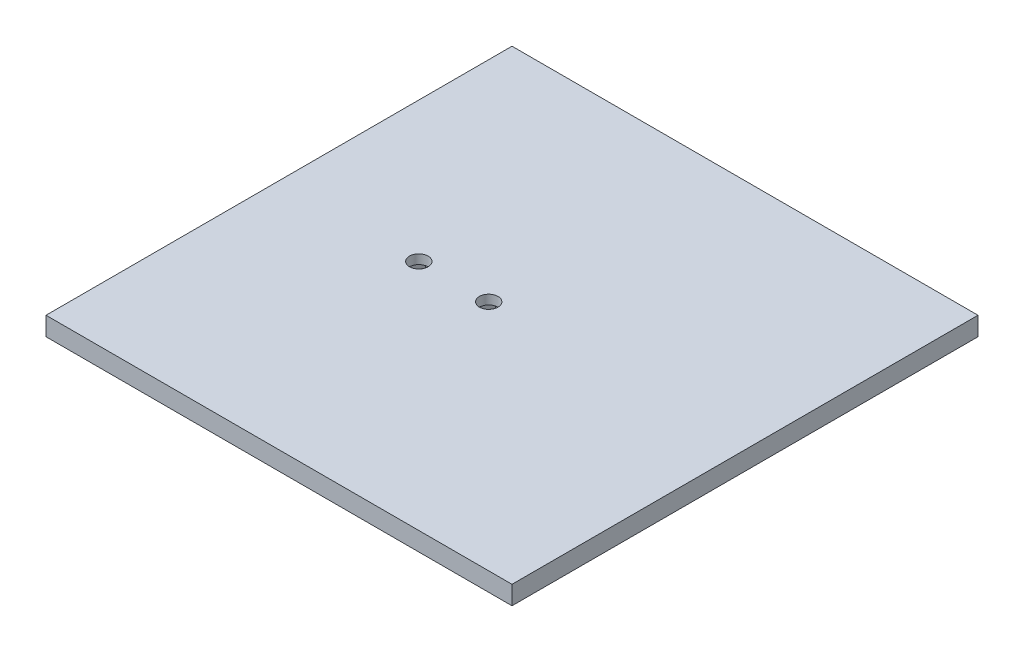
SolidWorks part; units mm, degrees
ref_plane "Front Plane" through (0, 0, 0) normal (0, 0, 1) x (1, 0, 0)
ref_plane "Top Plane" through (0, 0, 0) normal (0, 1, 0) x (1, 0, 0)
ref_plane "Right Plane" through (0, 0, 0) normal (1, 0, 0) x (0, 0, -1)
sketch "Sketch1" plane through (0, 0, 0) normal (0, 1, 0) x (1, 0, 0)
  line L1 (-34.8765, 23.534) -> (65.1235, 23.534)
  line L2 (-34.8765, 23.534) -> (-34.8765, -76.466)
  line L3 (-34.8765, -76.466) -> (65.1235, -76.466)
  line L4 (65.1235, 23.534) -> (65.1235, -76.466)
  point P22 (2.0874, -26.3153)
  dimension "D1" = 100
  dimension "D2" = 100
extrude "Boss-Extrude1" add sketch "Sketch1" along normal blind 4
sketch "Sketch3" plane through (0, 4, 0) normal (0, 1, 0) x (1, 0, 0)
  line L0 (-34.8765, -76.466) -> (65.1235, -76.466) construction
  line L1 (-34.8765, 23.534) -> (-34.8765, -76.466) construction
  circle A0 centre (-4.8765, -26.466) radius 2
  circle A1 centre (10.1235, -26.466) radius 2
  dimension "D5" = 4
  dimension "D6" = 4
  dimension "D1" = 50
  dimension "D2" = 50
  dimension "D3" = 30
  dimension "D4" = 15
extrude "Cut-Extrude1" cut sketch "Sketch3" against normal blind 2 contours A1 | A0
sketch "Sketch5" plane through (0, 0, 0) normal (0, -1, 0) x (1, 0, 0)
  line L0 (-34.8765, -23.534) -> (-34.8765, 76.466) construction
  line L1 (-0.8351, 26.466) -> (-2.8558, 29.966)
  line L2 (-2.8558, 29.966) -> (-6.8973, 29.966)
  line L3 (-6.8973, 29.966) -> (-8.918, 26.466)
  line L4 (-8.918, 26.466) -> (-6.8973, 22.966)
  line L5 (-6.8973, 22.966) -> (-2.8558, 22.966)
  line L6 (-2.8558, 22.966) -> (-0.8351, 26.466)
  line L7 (14.1649, 26.466) -> (12.1442, 29.966)
  line L8 (12.1442, 29.966) -> (8.1027, 29.966)
  line L9 (8.1027, 29.966) -> (6.082, 26.466)
  line L10 (6.082, 26.466) -> (8.1027, 22.966)
  line L11 (8.1027, 22.966) -> (12.1442, 22.966)
  line L12 (12.1442, 22.966) -> (14.1649, 26.466)
  line L13 (65.1235, -23.534) -> (-34.8765, -23.534) construction
  circle A0 centre (-4.8765, 26.466) radius 3.5 construction
  circle A1 centre (10.1235, 26.466) radius 3.5 construction
  point P18 (0, 0)
  point P19 (0, 0)
  dimension "D5" = 7
  dimension "D6" = 7
  dimension "D1" = 30
  dimension "D2" = 15
  dimension "D3" = 50
  dimension "D4" = 50
extrude "Cut-Extrude2" cut sketch "Sketch5" against normal blind 2
